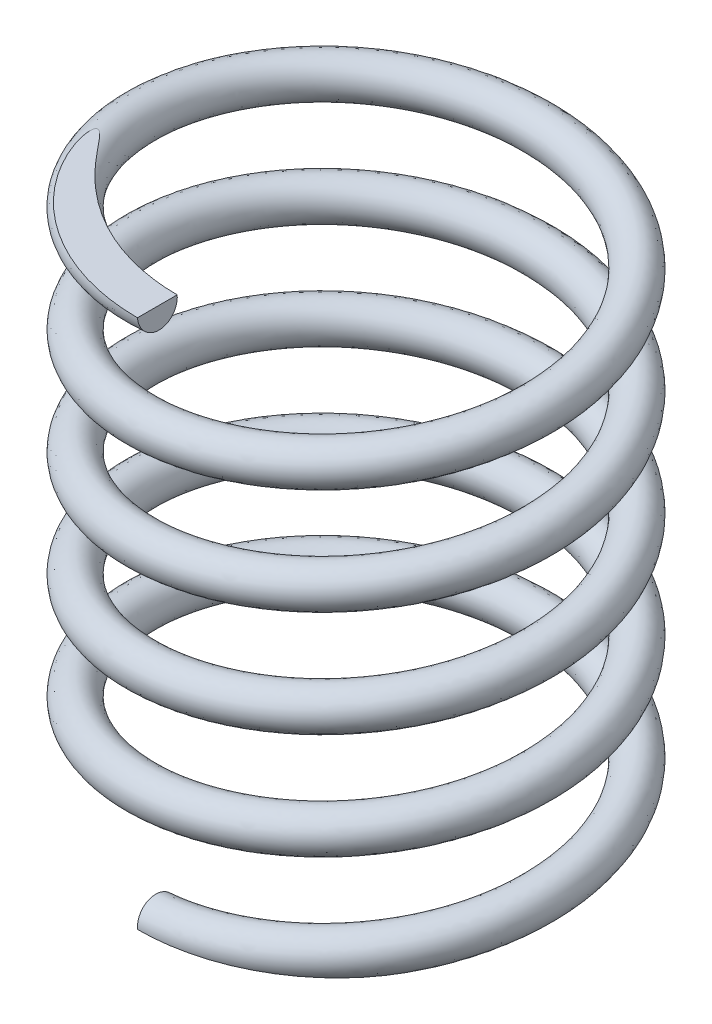
SolidWorks part; units mm, degrees
material "Пластичное железо (SN)"
ref_plane "Спереди" through (0, 0, 0) normal (0, 0, 1) x (1, 0, 0)
ref_plane "Сверху" through (0, 0, 0) normal (0, 1, 0) x (1, 0, 0)
ref_plane "Справа" through (0, 0, 0) normal (1, 0, 0) x (0, 0, -1)
sketch "Эскиз4" plane through (0, 0, 0) normal (0, 1, 0) x (1, 0, 0)
  circle A0 centre (0, 0) radius 7.5
  dimension "D1" = 15
curve "Спираль3" pitch 4 height 20 turns 5
ref_plane "Плоскость4" through (0, 0, 7.5) normal (0.9964, 0.0846, 0) x (0, 0, -1)
sketch "Эскиз5" plane through (0, 0, 7.5) normal (0.9964, 0.0846, 0) x (0, 0, -1)
  circle A0 centre (0, 0) radius 0.75
  dimension "D1" = 1.5
sweep "По траектории1" add profiles "Эскиз5" path "Спираль3"
ref_plane "Плоскость5" through (0, 0, 0) normal (0, 1, 0) x (1, 0, 0)
sketch "Эскиз6" plane through (0, 0, 0) normal (0, 1, 0) x (1, 0, 0)
  circle A0 centre (0, 0) radius 10.3377
  dimension "D1" = 20.6755
extrude "Вырез-Вытянуть1" cut sketch "Эскиз6" against normal blind 10
ref_plane "Плоскость6" through (0, 20, 0) normal (0, 1, 0) x (1, 0, 0)
sketch "Эскиз7" plane through (0, 20, 0) normal (0, 1, 0) x (1, 0, 0)
  circle A0 centre (0, 0) radius 10.1429
  dimension "D1" = 20.2859
extrude "Вырез-Вытянуть2" cut sketch "Эскиз7" along normal blind 10
